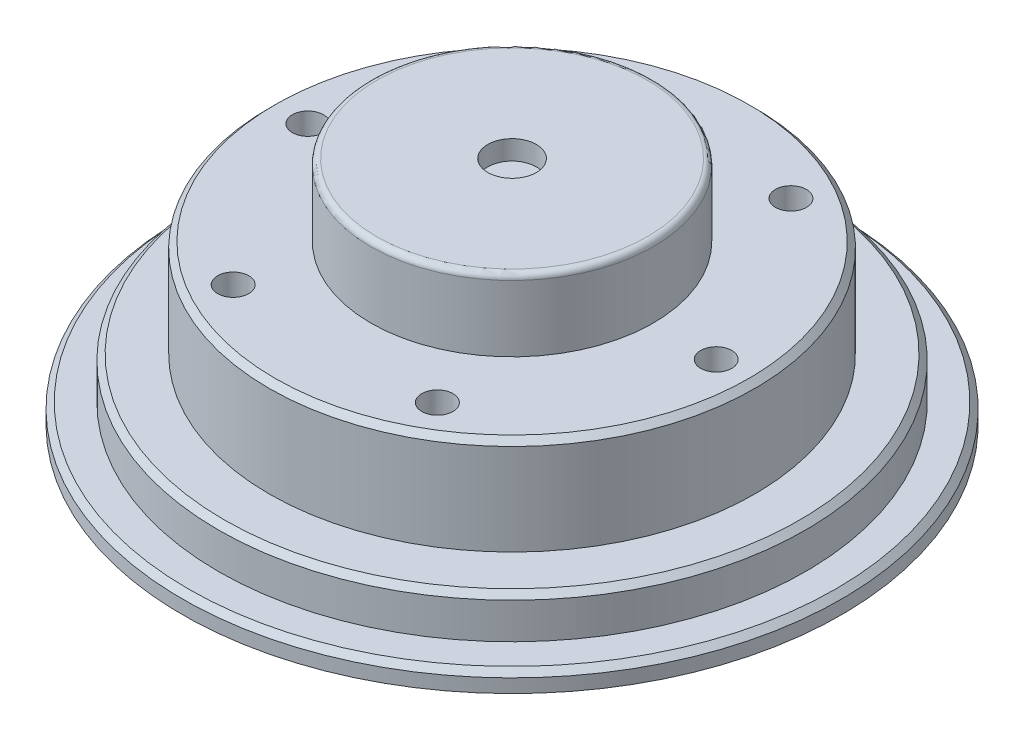
SolidWorks part; units mm, degrees
material "6061 合金"
ref_plane "前视基准面" through (0, 0, 0) normal (0, 0, 1) x (1, 0, 0)
ref_plane "上视基准面" through (0, 0, 0) normal (0, 1, 0) x (1, 0, 0)
ref_plane "右视基准面" through (0, 0, 0) normal (1, 0, 0) x (0, 0, -1)
sketch "草图1" plane through (0, 0, 0) normal (0, 1, 0) x (1, 0, 0)
  circle A0 centre (0, 0) radius 15.1
  dimension "D1" = 30.2
extrude "凸台-拉伸1" add sketch "草图1" along normal blind 2.15
sketch "草图2" plane through (0, 2.15, 0) normal (0, 1, 0) x (1, 0, 0)
  circle A0 centre (0, 0) radius 12.49
  dimension "D1" = 24.98
extrude "凸台-拉伸2" add sketch "草图2" along normal blind 5
sketch "草图3" plane through (0, 7.15, 0) normal (0, 1, 0) x (1, 0, 0)
  circle A0 centre (0, 0) radius 7.265
  dimension "D1" = 14.53
extrude "凸台-拉伸3" add sketch "草图3" along normal blind 3.7
sketch "草图4" plane through (0, 0, 0) normal (0, -1, 0) x (-1, 0, 0)
  circle A0 centre (0, 0) radius 16.95
  dimension "D1" = 33.9
extrude "凸台-拉伸4" add sketch "草图4" along normal blind 1
sketch "草图5" plane through (0, 10.85, 0) normal (0, 1, 0) x (1, 0, 0)
  circle A0 centre (0, 0) radius 1.25
  dimension "D1" = 2.5
extrude "切除-拉伸1" cut sketch "草图5" against normal blind 1
fillet "圆角1" radius 0.3 1 edges at (0, 10.85, 7.265)
chamfer "倒角1" distance 0.3 angle 45 3 edges at (0, 2.15, 15.1) (0, 7.15, 12.49) (0, 0, -16.95)
sketch "草图6" plane through (0, 7.15, 0) normal (0, 1, 0) x (1, 0, 0)
  line L1 (10.5, 0) -> (5.25, 9.0933) construction
  line L2 (5.25, 9.0933) -> (-5.25, 9.0933) construction
  line L3 (-5.25, 9.0933) -> (-10.5, 0) construction
  line L4 (-10.5, 0) -> (-5.25, -9.0933) construction
  line L5 (-5.25, -9.0933) -> (5.25, -9.0933) construction
  line L6 (5.25, -9.0933) -> (10.5, 0) construction
  circle A0 centre (0, 0) radius 10.5 construction
  dimension "D1" = 21
hole_wizard "M2 螺纹孔1" positions "草图7" profile "草图8" tap size "M2" standard "GB"
sketch "草图7" plane through (0, 7.15, 0) normal (0, 1, 0) x (1, 0, 0)
  point P0 (5.25, 9.0933)
  point P3 (10.5, 0)
  point P6 (5.25, -9.0933)
  point P9 (-5.25, -9.0933)
  point P12 (-10.5, 0)
  point P15 (-5.25, 9.0933)
sketch "草图8" plane through (5.25, 7.15, -9.0933) normal (1, 0, 0) x (0, 0, 1)
  line L0 (0, 0) -> (0, 5.6807)
  line L1 (0, 5.6807) -> (0.8, 5.2)
  line L2 (0.8, 5.2) -> (0.8, 0)
  line L5 (0.8, 0) -> (0, 0)
  line L10 (0, 5.6807) -> (-0.8, 5.2) construction
  line L11 (0, -6.35) -> (0, 107.95) construction
  dimension "螺纹孔钻头直径" = 1.6
  dimension "螺纹孔钻头深度" = 5.2
  dimension "导头角度" = 118
cosmetic thread "孔螺蚊线1" parameters "D1"=4, "D2"=2
cosmetic thread "孔螺蚊线2" parameters "D1"=4, "D2"=2
cosmetic thread "孔螺蚊线3" parameters "D1"=4, "D2"=2
cosmetic thread "孔螺蚊线4" parameters "D1"=4, "D2"=2
cosmetic thread "孔螺蚊线5" parameters "D1"=4, "D2"=2
cosmetic thread "孔螺蚊线6" parameters "D1"=4, "D2"=2
